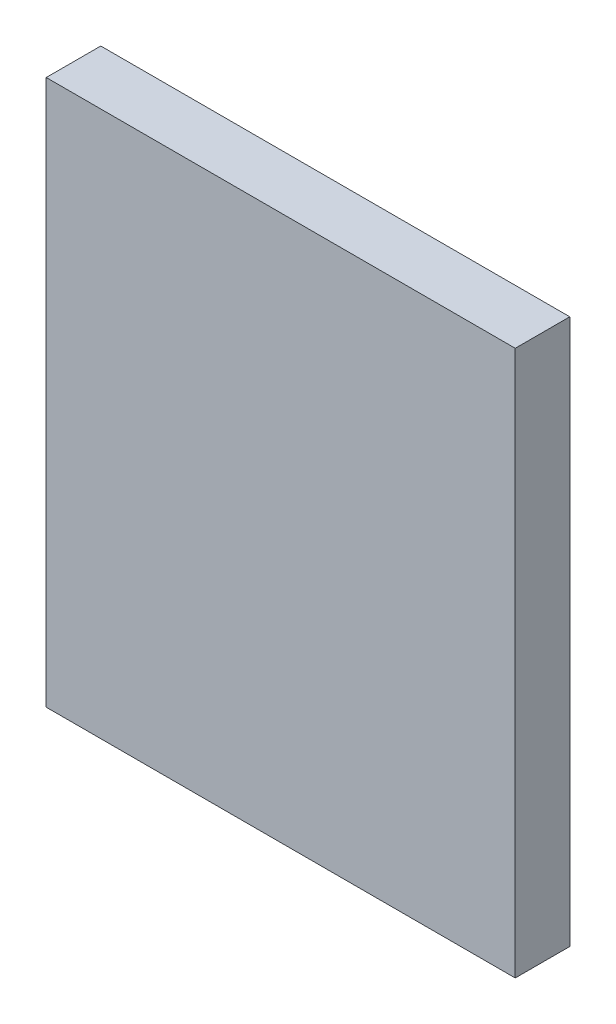
SolidWorks part; units mm, degrees
ref_plane "Front Plane" through (0, 0, 0) normal (0, 0, 1) x (1, 0, 0)
ref_plane "Top Plane" through (0, 0, 0) normal (0, 1, 0) x (1, 0, 0)
ref_plane "Right Plane" through (0, 0, 0) normal (1, 0, 0) x (0, 0, -1)
sketch "Sketch1" plane through (0, 0, 0) normal (0, 0, 1) x (1, 0, 0)
  line L1 (0, 0) -> (215, 0)
  line L2 (0, 0) -> (0, 250)
  line L3 (0, 250) -> (215, 250)
  line L4 (215, 0) -> (215, 250)
  dimension "D1" = 250
  dimension "D2" = 215
extrude "Boss-Extrude1" add sketch "Sketch1" along normal blind 25
